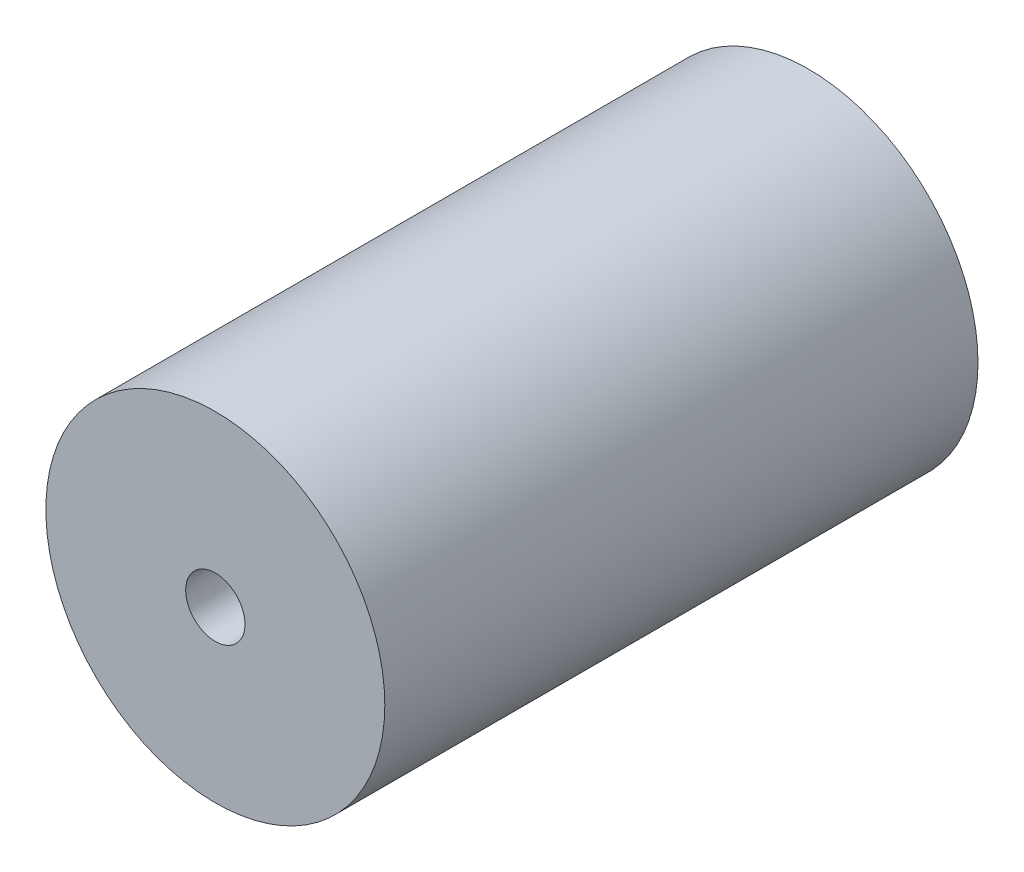
SolidWorks part; units mm, degrees
ref_plane "Front Plane" through (0, 0, 0) normal (0, 0, 1) x (1, 0, 0)
ref_plane "Top Plane" through (0, 0, 0) normal (0, 1, 0) x (1, 0, 0)
ref_plane "Right Plane" through (0, 0, 0) normal (1, 0, 0) x (0, 0, -1)
sketch "Sketch2" plane through (0, 0, 0) normal (0, 0, 1) x (1, 0, 0)
  circle A0 centre (0, 0) radius 100
  dimension "D1" = 200
extrude "Boss-Extrude1" add sketch "Sketch2" along normal mid plane 350
sketch "Sketch3" plane through (0, 0, -175) normal (0, 0, -1) x (-1, 0, 0)
  circle A0 centre (0, 0) radius 17.5
  dimension "D1" = 35
extrude "Cut-Extrude1" cut sketch "Sketch3" against normal through all both and the other way through all
